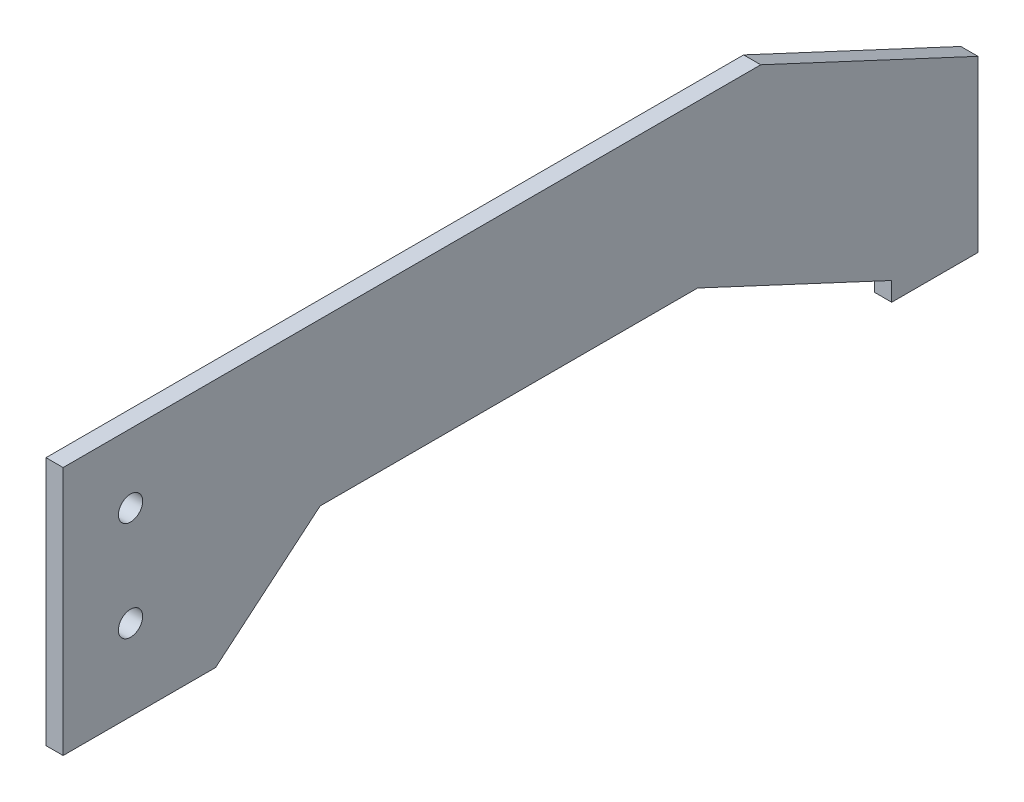
SolidWorks part; units mm, degrees
ref_plane "Front Plane" through (0, 0, 0) normal (0, 0, 1) x (1, 0, 0)
ref_plane "Top Plane" through (0, 0, 0) normal (0, 1, 0) x (1, 0, 0)
ref_plane "Right Plane" through (0, 0, 0) normal (1, 0, 0) x (0, 0, -1)
sketch "Sketch1" plane through (0, 0, 0) normal (1, 0, 0) x (0, 0, -1)
  line L1 (-70.0391, -1.219) -> (59.3225, -1.219)
  line L3 (-22.3885, -31.219) -> (47.6115, -31.219)
  line L7 (99.6115, -51.506) -> (99.6115, -20.006)
  line L8 (99.6115, -20.006) -> (59.3225, -1.219)
  line L11 (-41.7585, -47.4724) -> (-22.3885, -31.219)
  line L15 (-70.0391, -1.219) -> (-70.0391, -59.219) construction
  line L16 (59.3225, -1.219) -> (-70.0391, -1.219) construction
  line L24 (-70.0391, -1.219) -> (-70.0391, -47.4724)
  line L25 (-70.0391, -47.4724) -> (-41.7585, -47.4724)
  line L27 (-57.5385, -1.219) -> (-57.5385, -49.6208) construction
  line L28 (-70.0391, -13.9724) -> (-45.0379, -13.9724) construction
  line L29 (-70.0391, -32.4724) -> (-46.9512, -32.4724) construction
  line L30 (-55.7576, -59.219) -> (-22.3885, -31.219) construction
  line L31 (-22.3885, -31.219) -> (47.6115, -31.219) construction
  line L32 (99.6115, -20.006) -> (59.3225, -1.219) construction
  line L33 (99.6115, -60.006) -> (99.6115, -20.006) construction
  line L34 (99.6115, -51.506) -> (83.6115, -51.506)
  line L35 (83.6115, -48.006) -> (83.6115, -60.006) construction
  line L36 (83.6115, -51.506) -> (83.6115, -48.006)
  line L37 (83.6115, -48.006) -> (47.6115, -31.219)
  line L38 (-57.5385, -51.4709) -> (-57.5385, -93.4709) construction
  circle A0 centre (-57.5385, -13.9724) radius 2.25
  circle A1 centre (-57.5385, -32.4724) radius 2.25
  circle A2 centre (-57.5385, -32.4724) radius 2.25 construction
  dimension "D6" = 4.5
  dimension "D7" = 4.5
  dimension "D1" = 3.5
  dimension "D3" = 18.5
  dimension "D4" = 15
extrude "Boss-Extrude2" add sketch "Sketch1" along normal blind 3.175
